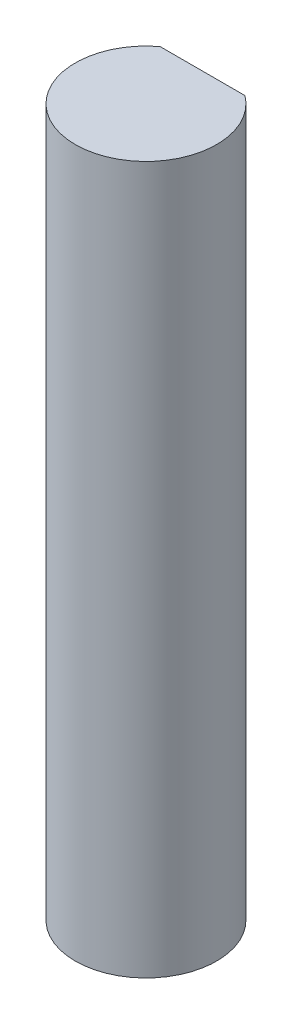
SolidWorks part; units mm, degrees
ref_plane "Front Plane" through (0, 0, 0) normal (0, 0, 1) x (1, 0, 0)
ref_plane "Top Plane" through (0, 0, 0) normal (0, 1, 0) x (1, 0, 0)
ref_plane "Right Plane" through (0, 0, 0) normal (1, 0, 0) x (0, 0, -1)
sketch "Sketch1" plane through (0, 0, 0) normal (0, 1, 0) x (1, 0, 0)
  line L0 (-1.905, 2.54) -> (1.905, 2.54)
  arc A0 (-1.905, 2.54) -> (1.905, 2.54) centre (0, 0) ccw
  dimension "D1" = 6.35
  dimension "D2" = 2.54
extrude "Boss-Extrude1" add sketch "Sketch1" along normal blind 31.75
